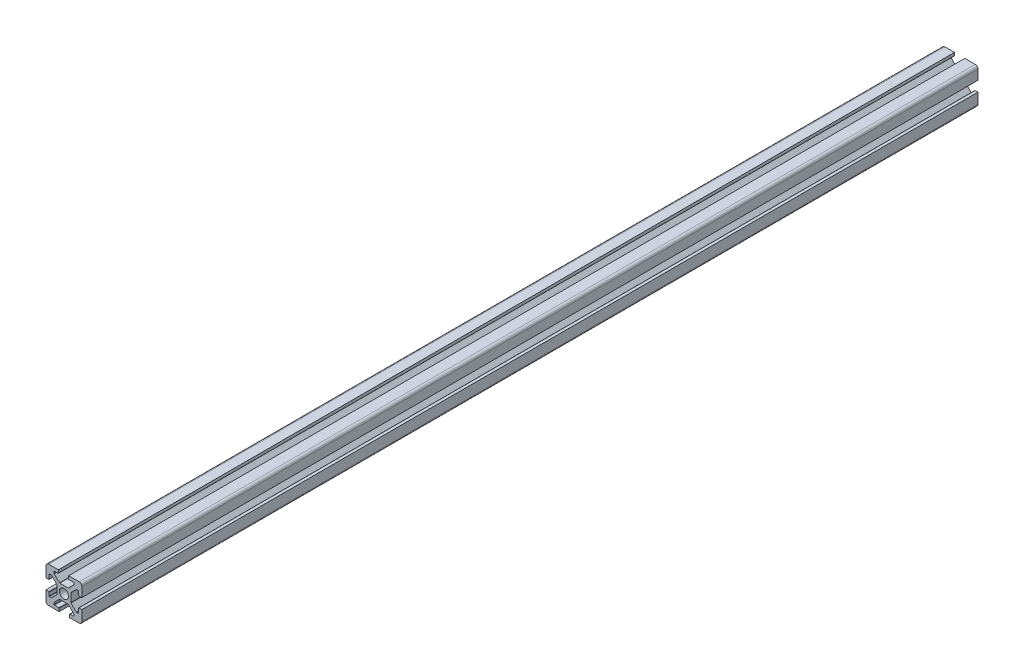
SolidWorks part; units mm, degrees
ref_plane "Front Plane" through (0, 0, 0) normal (0, 0, 1) x (1, 0, 0)
ref_plane "Top Plane" through (0, 0, 0) normal (0, 1, 0) x (1, 0, 0)
ref_plane "Right Plane" through (0, 0, 0) normal (1, 0, 0) x (0, 0, -1)
sketch "Sketch1" plane through (0, 0, 0) normal (0, 0, 1) x (1, 0, 0)
  line L1 (-8.5, -10) -> (-2.6476, -10)
  line L2 (-10, -8.5) -> (-10, -3.1)
  line L3 (-8.5, 10) -> (-3.1, 10)
  line L4 (10, -8.5) -> (10, -2.6476)
  line L5 (-1.8031, 1.8031) -> (1.8031, -1.8031) construction
  line L6 (-10, 10) -> (-3.9, 3.9) construction
  line L7 (2.3464, -3.9) -> (-2.3464, -3.9)
  line L8 (3.9, -2.3464) -> (3.9, 2.3464)
  line L9 (2.3464, 3.9) -> (-2.3464, 3.9)
  line L10 (-3.9, -2.3464) -> (-3.9, 2.3464)
  line L11 (1.8031, -1.8031) -> (-1.8031, 1.8031) construction
  line L12 (1.8031, 1.8031) -> (-1.8031, -1.8031) construction
  line L14 (-10, 2.6476) -> (-10, 8.5)
  line L15 (-10, 2.6476) -> (-8.45, 2.6476)
  line L17 (-10, -3.1) -> (-8.45, -3.1)
  line L18 (-3.9, 2.3464) -> (-3.9, -2.3464)
  line L19 (-8.2, 2.8976) -> (-8.2, 5.25)
  line L20 (-8.2, -3.35) -> (-8.2, -5.25)
  line L21 (-7.95, 5.5) -> (-7.0536, 5.5)
  line L22 (-6.8768, 5.4268) -> (-3.9732, 2.5232)
  line L23 (-6.8768, -5.4268) -> (-3.9732, -2.5232)
  line L24 (-7.95, -5.5) -> (-7.0536, -5.5)
  line L26 (-2.3464, 3.9) -> (2.3464, 3.9)
  line L27 (3.9, 3.9) -> (10, 10) construction
  line L28 (2.6476, 10) -> (2.6476, 8.45)
  line L29 (-3.1, 10) -> (-3.1, 8.45)
  line L30 (2.3464, 3.9) -> (-2.3464, 3.9)
  line L31 (2.8976, 8.2) -> (5.25, 8.2)
  line L32 (-3.35, 8.2) -> (-5.25, 8.2)
  line L33 (5.5, 7.95) -> (5.5, 7.0536)
  line L34 (5.4268, 6.8768) -> (2.5232, 3.9732)
  line L35 (-5.4268, 6.8768) -> (-2.5232, 3.9732)
  line L36 (-5.5, 7.95) -> (-5.5, 7.0536)
  line L37 (-1.8031, -1.8031) -> (1.8031, 1.8031) construction
  line L38 (3.9, 2.3464) -> (3.9, -2.3464)
  line L40 (10, -2.6476) -> (8.45, -2.6476)
  line L41 (10, 3.1) -> (8.45, 3.1)
  line L42 (3.9, -2.3464) -> (3.9, 2.3464)
  line L43 (8.2, -2.8976) -> (8.2, -5.25)
  line L44 (8.2, 3.35) -> (8.2, 5.25)
  line L45 (7.95, -5.5) -> (7.0536, -5.5)
  line L46 (6.8768, -5.4268) -> (3.9732, -2.5232)
  line L47 (6.8768, 5.4268) -> (3.9732, 2.5232)
  line L48 (7.95, 5.5) -> (7.0536, 5.5)
  line L50 (2.3464, -3.9) -> (-2.3464, -3.9)
  line L52 (-2.6476, -10) -> (-2.6476, -8.45)
  line L53 (3.1, -10) -> (3.1, -8.45)
  line L54 (-2.3464, -3.9) -> (2.3464, -3.9)
  line L55 (-2.8976, -8.2) -> (-5.25, -8.2)
  line L56 (3.35, -8.2) -> (5.25, -8.2)
  line L57 (-5.5, -7.95) -> (-5.5, -7.0536)
  line L58 (-5.4268, -6.8768) -> (-2.5232, -3.9732)
  line L59 (5.4268, -6.8768) -> (2.5232, -3.9732)
  line L60 (5.5, -7.95) -> (5.5, -7.0536)
  line L61 (2.6476, 10) -> (8.5, 10)
  line L62 (3.1, -10) -> (8.5, -10)
  line L63 (10, 3.1) -> (10, 8.5)
  line L65 (3.9, -3.9) -> (10, -10) construction
  circle A0 centre (0, 0) radius 2.55
  arc A1 (-8.2, -3.35) -> (-8.45, -3.1) centre (-8.45, -3.35) ccw
  arc A2 (-8.2, -5.25) -> (-7.95, -5.5) centre (-7.95, -5.25) ccw
  arc A3 (-6.8768, -5.4268) -> (-7.0536, -5.5) centre (-7.0536, -5.25) cw
  arc A4 (-3.9732, -2.5232) -> (-3.9, -2.3464) centre (-4.15, -2.3464) ccw
  arc A5 (-3.9, 2.3464) -> (-3.9732, 2.5232) centre (-4.15, 2.3464) ccw
  arc A6 (-7.0536, 5.5) -> (-6.8768, 5.4268) centre (-7.0536, 5.25) cw
  arc A7 (-8.2, 5.25) -> (-7.95, 5.5) centre (-7.95, 5.25) cw
  arc A8 (-8.2, 2.8976) -> (-8.45, 2.6476) centre (-8.45, 2.8976) cw
  arc A9 (-3.35, 8.2) -> (-3.1, 8.45) centre (-3.35, 8.45) ccw
  arc A10 (-5.25, 8.2) -> (-5.5, 7.95) centre (-5.25, 7.95) ccw
  arc A11 (-5.4268, 6.8768) -> (-5.5, 7.0536) centre (-5.25, 7.0536) cw
  arc A12 (-2.5232, 3.9732) -> (-2.3464, 3.9) centre (-2.3464, 4.15) ccw
  arc A13 (2.3464, 3.9) -> (2.5232, 3.9732) centre (2.3464, 4.15) ccw
  arc A14 (5.5, 7.0536) -> (5.4268, 6.8768) centre (5.25, 7.0536) cw
  arc A15 (5.25, 8.2) -> (5.5, 7.95) centre (5.25, 7.95) cw
  arc A16 (2.8976, 8.2) -> (2.6476, 8.45) centre (2.8976, 8.45) cw
  arc A17 (8.2, 3.35) -> (8.45, 3.1) centre (8.45, 3.35) ccw
  arc A18 (8.2, 5.25) -> (7.95, 5.5) centre (7.95, 5.25) ccw
  arc A19 (6.8768, 5.4268) -> (7.0536, 5.5) centre (7.0536, 5.25) cw
  arc A20 (3.9732, 2.5232) -> (3.9, 2.3464) centre (4.15, 2.3464) ccw
  arc A21 (3.9, -2.3464) -> (3.9732, -2.5232) centre (4.15, -2.3464) ccw
  arc A22 (7.0536, -5.5) -> (6.8768, -5.4268) centre (7.0536, -5.25) cw
  arc A23 (8.2, -5.25) -> (7.95, -5.5) centre (7.95, -5.25) cw
  arc A24 (8.2, -2.8976) -> (8.45, -2.6476) centre (8.45, -2.8976) cw
  arc A25 (3.35, -8.2) -> (3.1, -8.45) centre (3.35, -8.45) ccw
  arc A26 (5.25, -8.2) -> (5.5, -7.95) centre (5.25, -7.95) ccw
  arc A27 (5.4268, -6.8768) -> (5.5, -7.0536) centre (5.25, -7.0536) cw
  arc A28 (2.5232, -3.9732) -> (2.3464, -3.9) centre (2.3464, -4.15) ccw
  arc A29 (-2.3464, -3.9) -> (-2.5232, -3.9732) centre (-2.3464, -4.15) ccw
  arc A30 (-5.5, -7.0536) -> (-5.4268, -6.8768) centre (-5.25, -7.0536) cw
  arc A31 (-5.25, -8.2) -> (-5.5, -7.95) centre (-5.25, -7.95) cw
  arc A32 (-2.8976, -8.2) -> (-2.6476, -8.45) centre (-2.8976, -8.45) cw
  arc A33 (-10, -8.5) -> (-8.5, -10) centre (-8.5, -8.5) ccw
  arc A34 (8.5, -10) -> (10, -8.5) centre (8.5, -8.5) ccw
  arc A35 (10, 8.5) -> (8.5, 10) centre (8.5, 8.5) ccw
  arc A36 (-10, 8.5) -> (-8.5, 10) centre (-8.5, 8.5) cw
  point P15 (-10, -10)
  point P131 (0, 0)
  dimension "D1" = 20
  dimension "D4" = 5.1
  dimension "D5" = 0.25
  dimension "D6" = 1.5
  dimension "D2" = 20
  dimension "D3" = 4
extrude "Boss-Extrude1" add sketch "Sketch1" along normal blind 500 contours A36 L14 L15 A8 L19 A7 L21 A6 L22 A5 L10 A4 L23 A3 L24 A2 L20 A1 L17 L2 A33 L1 L52 A32 L55 A31 L57 A30 L58 A29 L7 A28 L59 A27 L60 A26 L56 A25 L53 L62 A34 L4 L40 A24 L43 A23 L45 A22 L46 A21 L8
